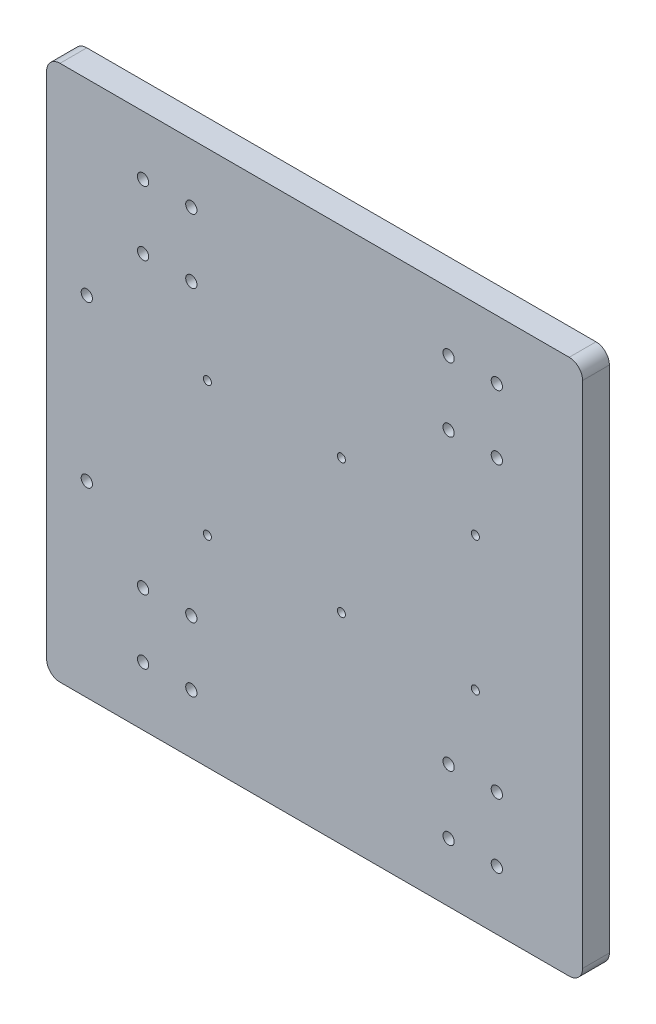
SolidWorks part; units mm, degrees
ref_plane "Front Plane" through (0, 0, 0) normal (0, 0, 1) x (1, 0, 0)
ref_plane "Top Plane" through (0, 0, 0) normal (0, 1, 0) x (1, 0, 0)
ref_plane "Right Plane" through (0, 0, 0) normal (1, 0, 0) x (0, 0, -1)
sketch "Model" plane through (0, 0, 0) normal (0, 0, 1) x (1, 0, 0)
  line L0 (-11, 0) -> (179, 0)
  line L1 (-16, 195) -> (-16, 5)
  line L2 (179, 200) -> (-11, 200)
  line L3 (184, 5) -> (184, 195)
  circle A0 centre (-1, 70) radius 2.1
  circle A1 centre (152, 178) radius 2.1
  circle A2 centre (152, 154) radius 2.1
  circle A3 centre (152, 22) radius 2.1
  circle A4 centre (152, 46) radius 2.1
  circle A5 centre (20, 178) radius 2.1
  circle A6 centre (38, 154) radius 2.1
  circle A7 centre (20, 22) radius 2.1
  circle A8 centre (38, 46) radius 2.1
  circle A9 centre (20, 46) radius 2.1
  circle A10 centre (38, 22) radius 2.1
  circle A11 centre (38, 178) radius 2.1
  circle A12 centre (20, 154) radius 2.1
  circle A13 centre (134, 46) radius 2.1
  circle A14 centre (134, 22) radius 2.1
  circle A15 centre (134, 154) radius 2.1
  circle A16 centre (134, 178) radius 2.1
  circle A17 centre (-1, 130) radius 2.1
  circle A18 centre (144, 125) radius 1.5
  circle A19 centre (144, 75) radius 1.5
  circle A20 centre (94, 125) radius 1.5
  circle A21 centre (94, 75) radius 1.5
  circle A22 centre (44, 125) radius 1.5
  circle A23 centre (44, 75) radius 1.5
  arc A24 (184, 195) -> (179, 200) centre (179, 195) ccw
  arc A25 (-11, 200) -> (-16, 195) centre (-11, 195) ccw
  arc A26 (-16, 5) -> (-11, 0) centre (-11, 5) ccw
  arc A27 (179, 0) -> (184, 5) centre (179, 5) ccw
sketch "Sketch2" plane through (0, 0, 0) normal (0, 0, 1) x (1, 0, 0)
  line L0 (-11, 0) -> (179, 0)
  line L1 (-16, 195) -> (-16, 5)
  line L2 (179, 200) -> (-11, 200)
  line L3 (184, 5) -> (184, 195)
  circle A0 centre (-1, 70) radius 2.1
  circle A1 centre (152, 178) radius 2.1
  circle A2 centre (152, 154) radius 2.1
  circle A3 centre (152, 22) radius 2.1
  circle A4 centre (152, 46) radius 2.1
  circle A5 centre (20, 178) radius 2.1
  circle A6 centre (38, 154) radius 2.1
  circle A7 centre (20, 22) radius 2.1
  circle A8 centre (38, 46) radius 2.1
  circle A9 centre (20, 46) radius 2.1
  circle A10 centre (38, 22) radius 2.1
  circle A11 centre (38, 178) radius 2.1
  circle A12 centre (20, 154) radius 2.1
  circle A13 centre (134, 46) radius 2.1
  circle A14 centre (134, 22) radius 2.1
  circle A15 centre (134, 154) radius 2.1
  circle A16 centre (134, 178) radius 2.1
  circle A17 centre (-1, 130) radius 2.1
  circle A18 centre (144, 125) radius 1.5
  circle A19 centre (144, 75) radius 1.5
  circle A20 centre (94, 125) radius 1.5
  circle A21 centre (94, 75) radius 1.5
  circle A22 centre (44, 125) radius 1.5
  circle A23 centre (44, 75) radius 1.5
  arc A24 (184, 195) -> (179, 200) centre (179, 195) ccw
  arc A25 (-11, 200) -> (-16, 195) centre (-11, 195) ccw
  arc A26 (-16, 5) -> (-11, 0) centre (-11, 5) ccw
  arc A27 (179, 0) -> (184, 5) centre (179, 5) ccw
extrude "Boss-Extrude1" add sketch "Sketch2" along normal blind 10
